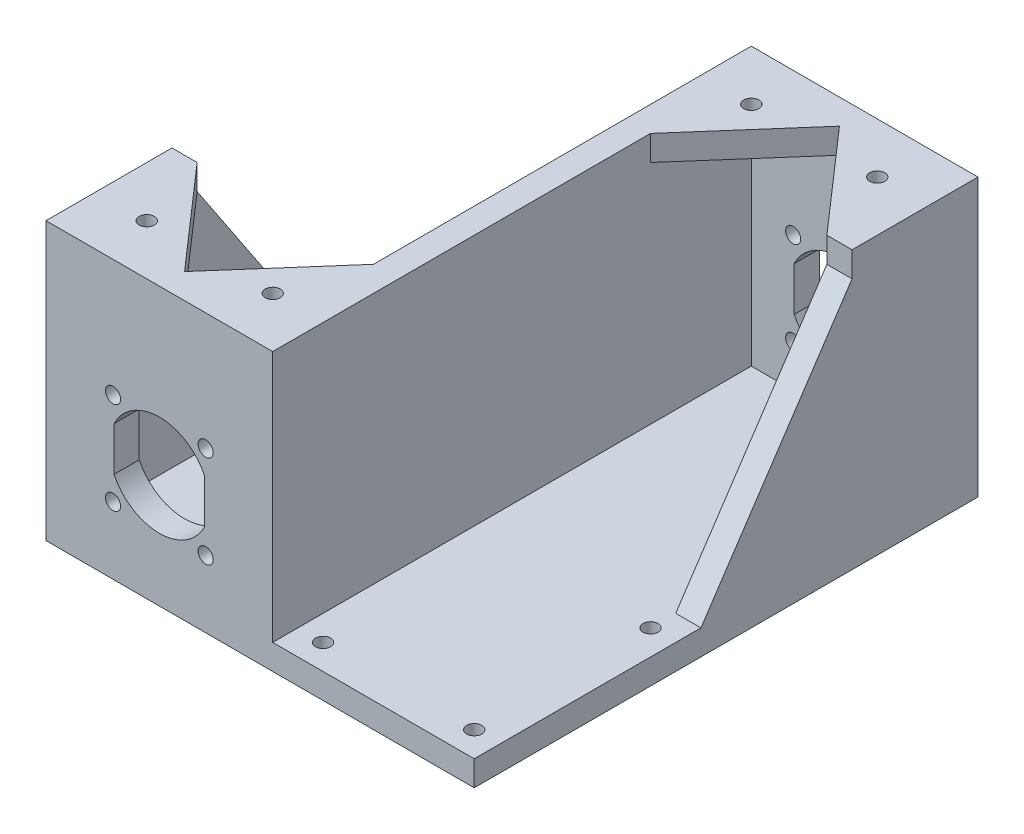
SolidWorks part; units mm, degrees
ref_plane "Plan de face" through (0, 0, 0) normal (0, 0, 1) x (1, 0, 0)
ref_plane "Plan de dessus" through (0, 0, 0) normal (0, 1, 0) x (1, 0, 0)
ref_plane "Plan de droite" through (0, 0, 0) normal (1, 0, 0) x (0, 0, -1)
sketch "Esquisse1" plane through (0, 0, 0) normal (0, 0, 1) x (1, 0, 0)
  line L0 (45, 0) -> (0, 45) construction
  line L1 (0, 0) -> (45, 0)
  line L2 (0, 0) -> (0, 45)
  line L3 (0, 45) -> (0, 55)
  line L4 (45, 0) -> (45, 45)
  line L5 (0, 0) -> (45, 45) construction
  line L6 (22.5, 45) -> (22.5, 0) construction
  line L7 (13.5, 26.8589) -> (13.5, 18.1411)
  line L8 (45, 22.5) -> (0, 22.5) construction
  line L9 (31.5, 26.8589) -> (31.5, 18.1411)
  line L10 (0, 55) -> (45, 55)
  line L11 (45, 55) -> (45, 45)
  line L12 (0, 45) -> (45, 45) construction
  arc A0 (13.5, 18.1411) -> (31.5, 18.1411) centre (22.5, 22.5) ccw
  circle A1 centre (31.6924, 31.6924) radius 1.5
  circle A2 centre (31.6924, 13.3076) radius 1.5
  circle A3 centre (13.3076, 13.3076) radius 1.5
  circle A4 centre (13.3076, 31.6924) radius 1.5
  arc A5 (31.5, 26.8589) -> (13.5, 26.8589) centre (22.5, 22.5) ccw
  dimension "D3" = 20
  dimension "D5" = 3
  dimension "D1" = 45
  dimension "D2" = 45
  dimension "D4" = 13
  dimension "D6" = 9
  dimension "D7" = 55
extrude "Extrusion1" add sketch "Esquisse1" along normal blind 5
sketch "Esquisse2" plane through (0, 0, 5) normal (0, 0, 1) x (1, 0, 0)
  line L0 (45, 0) -> (45, 55) construction
  line L1 (0, 0) -> (45, 0)
  line L2 (0, 0) -> (0, 5)
  line L3 (0, 5) -> (45, 5)
  line L4 (45, 0) -> (45, 5)
  dimension "D1" = 5
extrude "Extrusion2" add sketch "Esquisse2" along normal blind 95
sketch "Esquisse3" plane through (45, 0, 0) normal (1, 0, 0) x (0, 0, -1)
  line L0 (-5, 5) -> (-5, 55)
  line L1 (-25, 50) -> (-55, 5)
  line L2 (-100, 5) -> (-5, 5) construction
  line L3 (-55, 5) -> (-5, 5)
  line L4 (-25, 55) -> (-5, 55)
  line L7 (-25, 50) -> (-25, 55)
  dimension "D1" = 50
  dimension "D2" = 20
  dimension "D3" = 5
extrude "Extrusion3" add sketch "Esquisse3" against normal blind 5
sketch "Esquisse4" plane through (0, 0, 0) normal (-1, 0, 0) x (0, 0, 1)
  line L0 (5, 5) -> (5, 55)
  line L1 (5, 55) -> (100, 55)
  line L2 (100, 55) -> (100, 5)
  line L3 (100, 5) -> (5, 5)
  line L4 (5, 55) -> (0, 55) construction
  line L5 (5, 55) -> (5, 5) construction
extrude "Extrusion4" add sketch "Esquisse4" against normal blind 5
sketch "Esquisse5" plane through (0, 0, 0) normal (-1, 0, 0) x (0, 0, 1)
  line L0 (100, 55) -> (100, 0) construction
  line L1 (0, 0) -> (100, 0)
  line L2 (0, 0) -> (0, 5)
  line L3 (0, 5) -> (100, 5)
  line L4 (100, 0) -> (100, 5)
  dimension "D1" = 5
extrude "Extrusion5" add sketch "Esquisse5" along normal blind 40
sketch "Esquisse6" plane through (0, 0, 100) normal (0, 0, 1) x (1, 0, 0)
  line L0 (0, 5) -> (0, 55)
  line L1 (0, 55) -> (-40, 55)
  line L2 (-40, 55) -> (-40, 5)
  line L3 (-40, 5) -> (0, 5)
  line L4 (0, 55) -> (0, 5) construction
  dimension "D1" = 50
extrude "Extrusion6" add sketch "Esquisse6" against normal blind 5
sketch "Esquisse7" plane through (-40, 0, 0) normal (-1, 0, 0) x (0, 0, 1)
  line L0 (95, 5) -> (95, 55)
  line L1 (95, 55) -> (100, 55) construction
  line L2 (95, 5) -> (0, 5) construction
  line L3 (45, 5) -> (95, 5)
  line L6 (95, 55) -> (75, 55)
  line L7 (75, 55) -> (75, 50)
  line L8 (75, 50) -> (45, 5)
  dimension "D1" = 50
  dimension "D2" = 20
  dimension "D3" = 5
extrude "Extrusion7" add sketch "Esquisse7" against normal blind 5
sketch "Esquisse8" plane through (0, 0, 100) normal (0, 0, 1) x (1, 0, 0)
  line L0 (5, 5) -> (5, 0) construction
  line L1 (-40, 0) -> (45, 0) construction
  line L2 (-40, 45) -> (-40, 0) construction
  line L4 (-40, 45) -> (5, 45) construction
  line L5 (-26.5, 18.1411) -> (-26.5, 26.8589)
  line L8 (-40, 0) -> (5, 45) construction
  line L9 (-8.5, 18.1411) -> (-8.5, 26.8589)
  line L10 (5, 55) -> (-40, 55) construction
  line L11 (-17.5, 55) -> (-17.5, 0) construction
  line L13 (-40, 45) -> (5, 0) construction
  line L14 (5, 5) -> (5, 55) construction
  arc A0 (-26.5, 18.1411) -> (-8.5, 18.1411) centre (-17.5, 22.5) ccw
  circle A1 centre (-8.3076, 13.3076) radius 1.5
  circle A2 centre (-8.3076, 31.6924) radius 1.5
  circle A3 centre (-26.6924, 31.6924) radius 1.5
  circle A4 centre (-26.6924, 13.3076) radius 1.5
  arc A5 (-8.5, 26.8589) -> (-26.5, 26.8589) centre (-17.5, 22.5) ccw
  dimension "D1" = 20
  dimension "D2" = 3
  dimension "D6" = 3
  dimension "D3" = 13
  dimension "D4" = 9
  dimension "D5" = 45
  dimension "D7" = 13
extrude "Enlèv. mat.-Extru.1" cut sketch "Esquisse8" against normal up to next
sketch "Esquisse9" plane through (0, 5, 0) normal (0, 1, 0) x (-1, 0, 0)
  line L0 (-45, 100) -> (-5, 100) construction
  line L1 (-45, 100) -> (-45, 55) construction
  line L2 (40, 0) -> (0, 0) construction
  line L3 (40, 45) -> (40, 0) construction
  circle A0 centre (-40, 95) radius 1.5
  circle A1 centre (-10, 95) radius 1.5
  circle A2 centre (35, 5) radius 1.5
  circle A3 centre (5, 5) radius 1.5
  circle A4 centre (-40, 60) radius 1.5
  circle A5 centre (35, 40) radius 1.5
  dimension "D1" = 3
  dimension "D2" = 3
  dimension "D4" = 5
  dimension "D6" = 35
  dimension "D7" = 5
  dimension "D9" = 3
  dimension "D10" = 3
  dimension "D13" = 3
  dimension "D16" = 3
  dimension "D17" = 40
  dimension "D18" = 5
  dimension "D3" = 5
  dimension "D5" = 5
  dimension "D8" = 5
  dimension "D11" = 35
  dimension "D12" = 5
  dimension "D14" = 5
  dimension "D15" = 40
extrude "Enlèv. mat.-Extru.2" cut sketch "Esquisse9" against normal up to next
sketch "Esquisse11" plane through (0, 55, 0) normal (0, 1, 0) x (1, 0, 0)
  line L0 (22.5, -5) -> (5, -25)
  line L2 (5, -100) -> (5, -5) construction
  line L3 (45, 0) -> (0, 0) construction
  line L4 (5, -25) -> (5, 0)
  line L5 (40, -5) -> (5, -5) construction
  line L6 (5, 0) -> (40, 0)
  line L7 (40, 0) -> (40, -25)
  line L8 (40, -25) -> (22.5, -5)
  dimension "D1" = 25
extrude "Boss.-Extru.1" add sketch "Esquisse11" against normal blind 5
sketch "Esquisse12" plane through (0, 55, 0) normal (0, 1, 0) x (1, 0, 0)
  line L0 (0, -75) -> (-17.5, -95)
  line L1 (0, -95) -> (0, 0) construction
  line L2 (0, -95) -> (-35, -95) construction
  line L3 (0, -75) -> (0, -100)
  line L4 (5, -100) -> (-40, -100) construction
  line L5 (0, -95) -> (-35, -95) construction
  line L6 (0, -100) -> (-35, -100)
  line L7 (-35, -100) -> (-35, -75)
  line L8 (-35, -75) -> (-17.5, -95)
  dimension "D1" = 25
extrude "Boss.-Extru.2" add sketch "Esquisse12" against normal blind 5
sketch "Esquisse16" plane through (0, 55, 0) normal (0, 1, 0) x (1, 0, 0)
  line L0 (-40, -75) -> (-40, -100) construction
  line L1 (5, -100) -> (-40, -100) construction
  line L2 (5, -100) -> (5, -25) construction
  line L3 (0, -75) -> (0, 0) construction
  line L4 (45, 0) -> (0, 0) construction
  line L5 (45, -25) -> (45, 0) construction
  circle A0 centre (-5, -90) radius 1.5
  circle A1 centre (-30, -90) radius 1.5
  circle A2 centre (10, -10) radius 1.5
  circle A3 centre (35, -10) radius 1.5
  dimension "D1" = 10
  dimension "D3" = 3
  dimension "D6" = 3
  dimension "D7" = 3
  dimension "D8" = 10
  dimension "D9" = 10
  dimension "D12" = 3
  dimension "D2" = 10
  dimension "D4" = 10
  dimension "D5" = 10
  dimension "D10" = 10
  dimension "D11" = 10
extrude "Enlèv. mat.-Extru.3" cut sketch "Esquisse16" against normal blind 4
